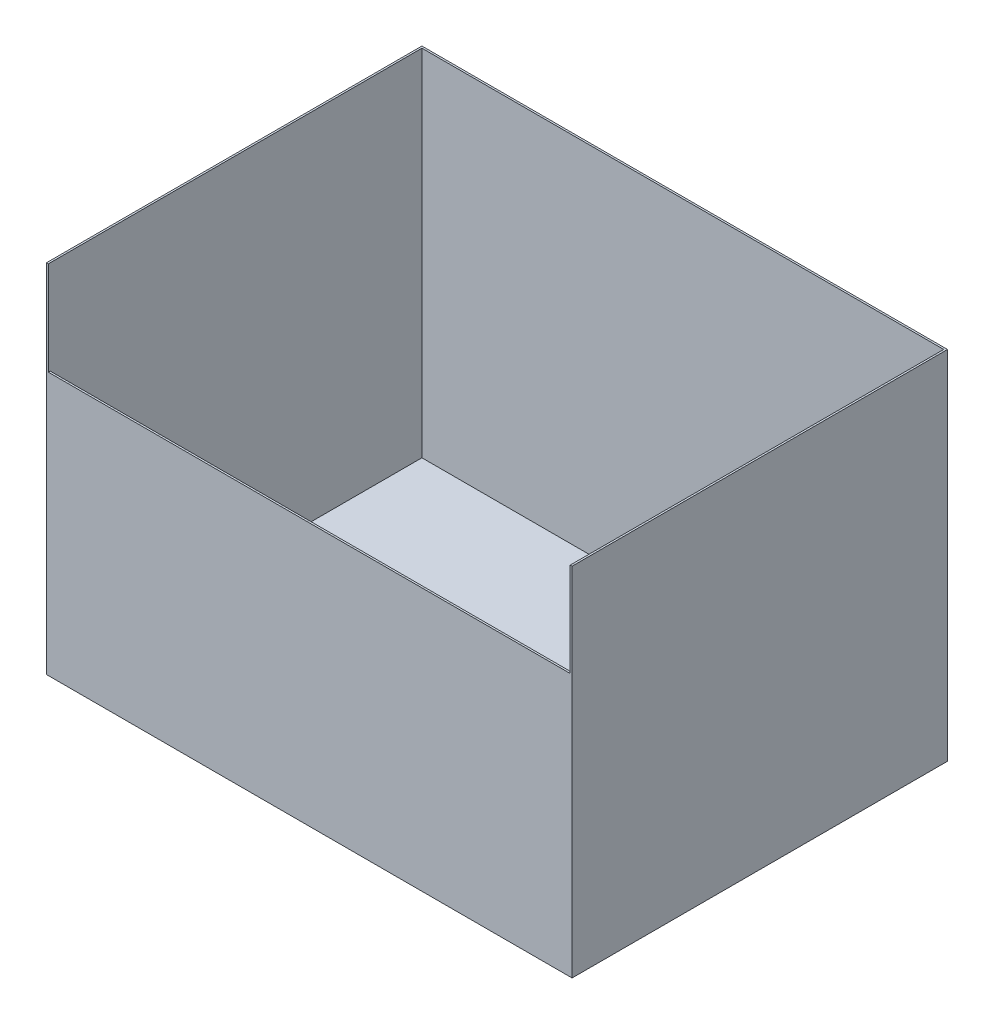
SolidWorks part; units mm, degrees
ref_plane "Front Plane" through (0, 0, 0) normal (0, 0, 1) x (1, 0, 0)
ref_plane "Top Plane" through (0, 0, 0) normal (0, 1, 0) x (1, 0, 0)
ref_plane "Right Plane" through (0, 0, 0) normal (1, 0, 0) x (0, 0, -1)
sketch "Sketch1" plane through (0, 0, 0) normal (0, 1, 0) x (1, 0, 0)
  line L0 (-355.6, 254) -> (355.6, -254) construction
  line L1 (-355.6, 254) -> (355.6, 254)
  line L2 (-355.6, 254) -> (-355.6, -254)
  line L3 (-355.6, -254) -> (355.6, -254)
  line L4 (355.6, 254) -> (355.6, -254)
  dimension "D1" = 711.2
  dimension "D2" = 508
extrude "Boss-Extrude1" add sketch "Sketch1" along normal mid plane 482.6
shell "Shell1" thickness 2.54
sketch "Sketch2" plane through (0, 0, 254) normal (0, 0, 1) x (1, 0, 0)
  line L0 (-355.6, 241.3) -> (-355.6, -241.3) construction
  line L1 (-353.06, 241.3) -> (353.06, 241.3)
  line L2 (-353.06, 241.3) -> (-353.06, 114.3)
  line L3 (-353.06, 114.3) -> (353.06, 114.3)
  line L4 (353.06, 241.3) -> (353.06, 114.3)
  line L5 (355.6, 241.3) -> (355.6, -241.3) construction
  line L6 (-355.6, 241.3) -> (355.6, 241.3) construction
  dimension "D1" = 127
  dimension "D2" = 2.54
  dimension "D3" = 2.54
extrude "Cut-Extrude1" cut sketch "Sketch2" against normal up to next
